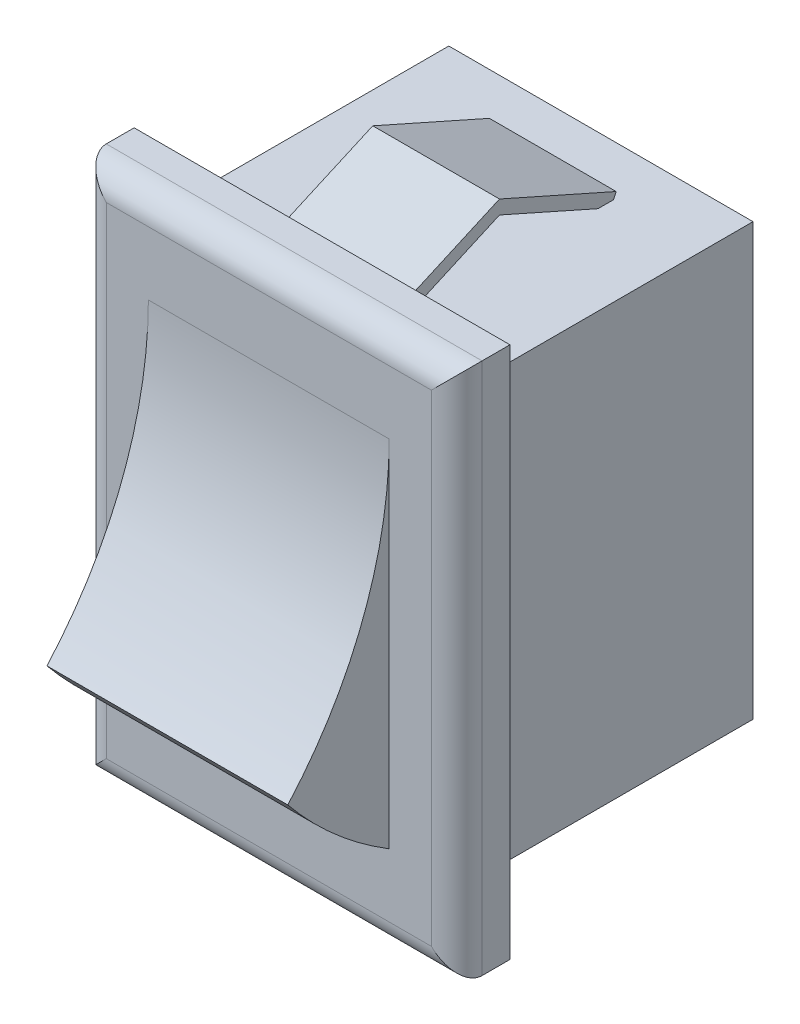
SolidWorks part; units mm, degrees
ref_plane "Face" through (0, 0, 0) normal (0, 0, 1) x (1, 0, 0)
ref_plane "Dessus" through (0, 0, 0) normal (0, 1, 0) x (1, 0, 0)
ref_plane "Droite" through (0, 0, 0) normal (1, 0, 0) x (0, 0, -1)
sketch "Esquisse1" plane through (0, 0, 0) normal (0, 0, 1) x (1, 0, 0)
  line L1 (-6, -8.5) -> (6, -8.5)
  line L2 (-6, -8.5) -> (-6, 8.5)
  line L3 (-6, 8.5) -> (6, 8.5)
  line L4 (6, -8.5) -> (6, 8.5)
  line L5 (-6, -8.5) -> (6, 8.5) construction
  line L6 (-6, 8.5) -> (6, -8.5) construction
  point P4 (0, 0)
  dimension "D1" = 17
  dimension "D2" = 12
extrude "Boss.-Extru.1" add sketch "Esquisse1" along normal blind 11
sketch "Esquisse2" plane through (0, 0, 11) normal (0, 0, 1) x (1, 0, 0)
  line L0 (-6, 8.5) -> (6, -8.5) construction
  line L2 (-7.4118, -10.5) -> (7.4118, -10.5)
  line L3 (-7.4118, -10.5) -> (-7.4118, 10.5)
  line L4 (-7.4118, 10.5) -> (7.4118, 10.5)
  line L5 (7.4118, -10.5) -> (7.4118, 10.5)
  line L6 (-7.4118, -10.5) -> (7.4118, 10.5) construction
  line L7 (-7.4118, 10.5) -> (7.4118, -10.5) construction
  point P4 (0, 0)
  dimension "D1" = 21
extrude "Boss.-Extru.2" add sketch "Esquisse2" along normal blind 2.1
sketch "Esquisse3" plane through (0, 0, 0) normal (1, 0, 0) x (0, 0, -1)
  line L0 (-28.8813, 7) -> (-13.1, 7) construction
  line L1 (-13.1, -10.5) -> (-13.1, 10.5) construction
  line L2 (-17.1, -3.5) -> (-13.1, -3.5) construction
  line L3 (-13.1, -10.5) -> (-11, -10.5) construction
  line L4 (-13.1, 7) -> (-13.1, 10.5) construction
  line L5 (-13.1, -7) -> (-13.1, -10.5) construction
  line L6 (-13.1, 10.5) -> (-11, 10.5) construction
  line L7 (-13.1, -7) -> (-13.1, 7)
  arc A0 (-17.1, -3.5) -> (-13.1, 7) centre (-28.8813, 7) ccw
  arc A1 (-17.1, -3.5) -> (-13.1, -7) centre (-4.8564, 6.457) ccw
  point P12 (-13.1, -7)
  dimension "D1" = 4
  dimension "D2" = 7
  dimension "D3" = 3.5
extrude "Boss.-Extru.3" add sketch "Esquisse3" along normal mid plane 9.5
sketch "Esquisse4" plane through (0, 0, 0) normal (1, 0, 0) x (0, 0, -1)
  line L0 (-11, -8.5) -> (-6.5, -10.5)
  line L1 (-6.5, -10.5) -> (-2, -8.5)
  line L2 (-11, -8.5) -> (0, -8.5) construction
  line L3 (-11, 8.5) -> (-6.5, 10.5)
  line L4 (-6.5, 10.5) -> (-2, 8.5)
  line L5 (-11, 8.5) -> (0, 8.5) construction
  line L6 (-11, -10.5) -> (-11, 10.5) construction
  dimension "D1" = 4.5
  dimension "D2" = 6.5
  dimension "D3" = 2
  dimension "D4" = 9
extrude "Extru.-Mince1" add sketch "Esquisse4" along normal mid plane 5 thin thin type mid plane wall 0.5
fillet "Congé1" radius 1 4 edges at (0, -10.5, 13.1) (-7.4118, 0, 13.1) (7.4118, 0, 13.1) (0, 10.5, 13.1)
